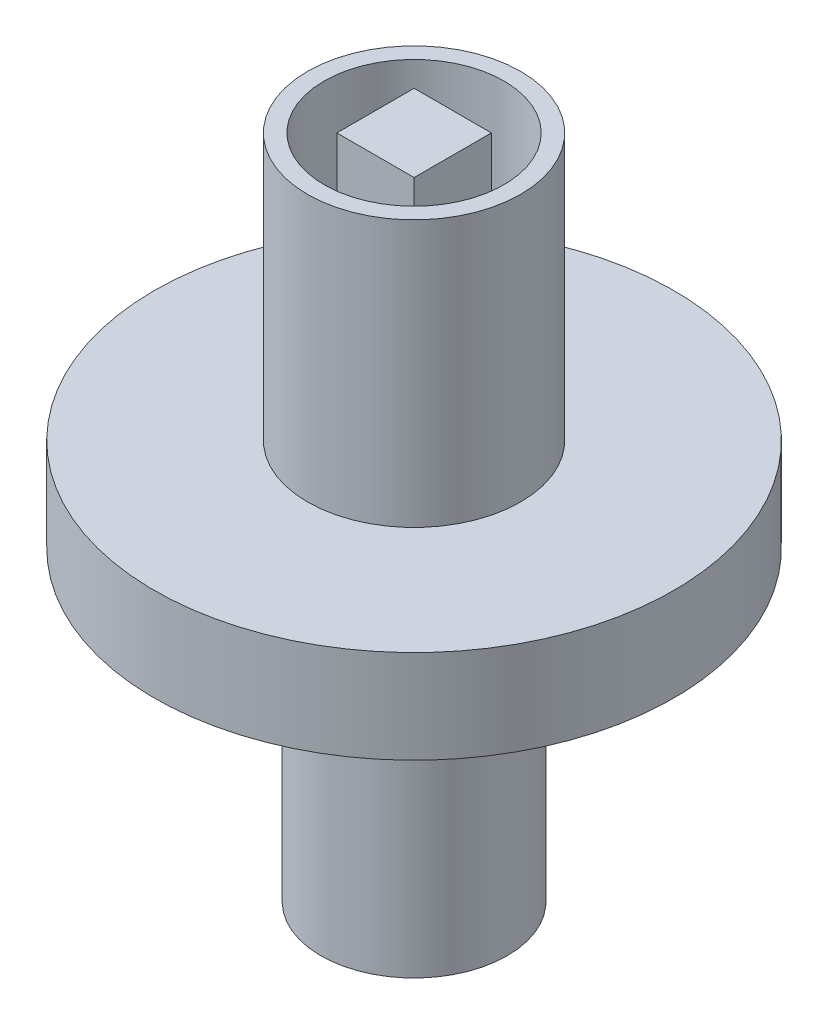
SolidWorks part; units mm, degrees
material "ABS"
ref_plane "Front Plane" through (0, 0, 0) normal (0, 0, 1) x (1, 0, 0)
ref_plane "Top Plane" through (0, 0, 0) normal (0, 1, 0) x (1, 0, 0)
ref_plane "Right Plane" through (0, 0, 0) normal (1, 0, 0) x (0, 0, -1)
sketch "Sketch1" plane through (0, 0, 0) normal (0, 0, 1) x (1, 0, 0)
  line L0 (0, 96.2797) -> (0, -99.3784) construction
  line L1 (-49.1359, 0) -> (108.8957, 0) construction
sketch "Sketch2" plane through (0, 0, 0) normal (0, 0, 1) x (1, 0, 0)
  line L0 (-49.1359, 0) -> (108.8957, 0) construction
  line L1 (19.5, 0) -> (19.5, 7)
  line L2 (19.5, 7) -> (8, 7)
  line L3 (8, 7) -> (8, 27)
  line L4 (8, 27) -> (0, 27)
  line L5 (0, 96.2797) -> (0, -99.3784) construction
  line L6 (0, 27) -> (0, 0)
  line L7 (0, 0) -> (19.5, 0)
  dimension "D1" = 19.5
  dimension "D2" = 8
  dimension "D3" = 7
  dimension "D4" = 20
revolve "Revolve2" add sketch "Sketch2" angle 360 about L0
sketch "Sketch3" plane through (0, 27, 0) normal (0, 1, 0) x (1, 0, 0)
  circle A0 centre (0, 0) radius 6.75
  dimension "D1" = 13.5
extrude "Cut-Extrude1" cut sketch "Sketch3" against normal blind 15 contours A0
sketch "Sketch4" plane through (0, 12, 0) normal (0, 1, 0) x (1, 0, 0)
  line L1 (-2.8952, 2.8974) -> (2.9048, 2.8974)
  line L2 (-2.8952, 2.8974) -> (-2.8952, -2.9026)
  line L3 (-2.8952, -2.9026) -> (2.9048, -2.9026)
  line L4 (2.9048, 2.8974) -> (2.9048, -2.9026)
  point P6 (0.0048, -0.0026)
extrude "Boss-Extrude1" add sketch "Sketch4" along normal blind 15
sketch "Sketch6" plane through (0, 0, 0) normal (0, -1, 0) x (1, 0, 0)
  circle A0 centre (0, 0) radius 7
  dimension "D1" = 14
extrude "Boss-Extrude2" add sketch "Sketch6" along normal blind 23
sketch "Sketch7" plane through (0, -23, 0) normal (0, -1, 0) x (1, 0, 0)
  circle A0 centre (0, 0) radius 3.5
  dimension "D1" = 7
extrude "Cut-Extrude2" cut sketch "Sketch7" against normal blind 15
sketch "Sketch8" plane through (0, -23, 0) normal (0, -1, 0) x (1, 0, 0)
  line L4 (-5.3, 1.5) -> (-1.5, 1.5)
  line L5 (-5.3, 1.5) -> (-5.3, -1.5)
  line L6 (5.3, 1.5) -> (5.3, -1.5)
  line L7 (-5.3, -1.5) -> (-1.5, -1.5)
  line L8 (-1.5, -5.3) -> (-1.5, -1.5)
  line L9 (-1.5, -5.3) -> (1.5, -5.3)
  line L10 (-1.5, 5.3) -> (1.5, 5.3)
  line L11 (1.5, -5.3) -> (1.5, -1.5)
  line L12 (1.5, 1.5) -> (5.3, 1.5)
  line L13 (1.5, 1.5) -> (1.5, 5.3)
  line L14 (1.5, -1.5) -> (5.3, -1.5)
  line L15 (-1.5, 1.5) -> (-1.5, 5.3)
  point P1 (0, 0)
  point P2 (0, 0)
  point P3 (0, 0)
  dimension "D1" = 10.6
  dimension "D2" = 3
  dimension "D3" = 10.6
  dimension "D4" = 3
extrude "Cut-Extrude3" cut sketch "Sketch8" against normal blind 15
